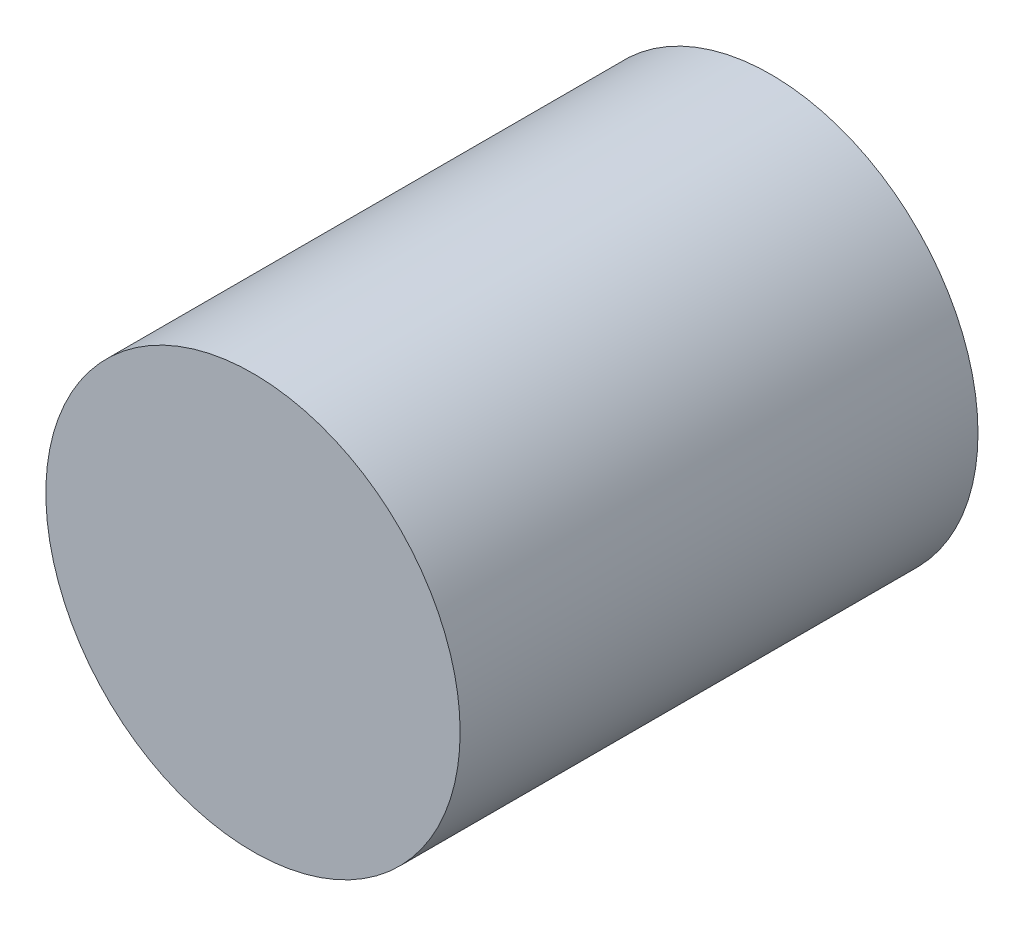
SolidWorks part; units mm, degrees
material "AISI 1020"
ref_plane "Front Plane" through (0, 0, 0) normal (0, 0, 1) x (1, 0, 0)
ref_plane "Top Plane" through (0, 0, 0) normal (0, 1, 0) x (1, 0, 0)
ref_plane "Right Plane" through (0, 0, 0) normal (1, 0, 0) x (0, 0, -1)
sketch "Sketch1" plane through (0, 0, 0) normal (0, 0, 1) x (1, 0, 0)
  circle A0 centre (0, 0) radius 20
  dimension "D1" = 40
extrude "Boss-Extrude1" add sketch "Sketch1" along normal blind 50
